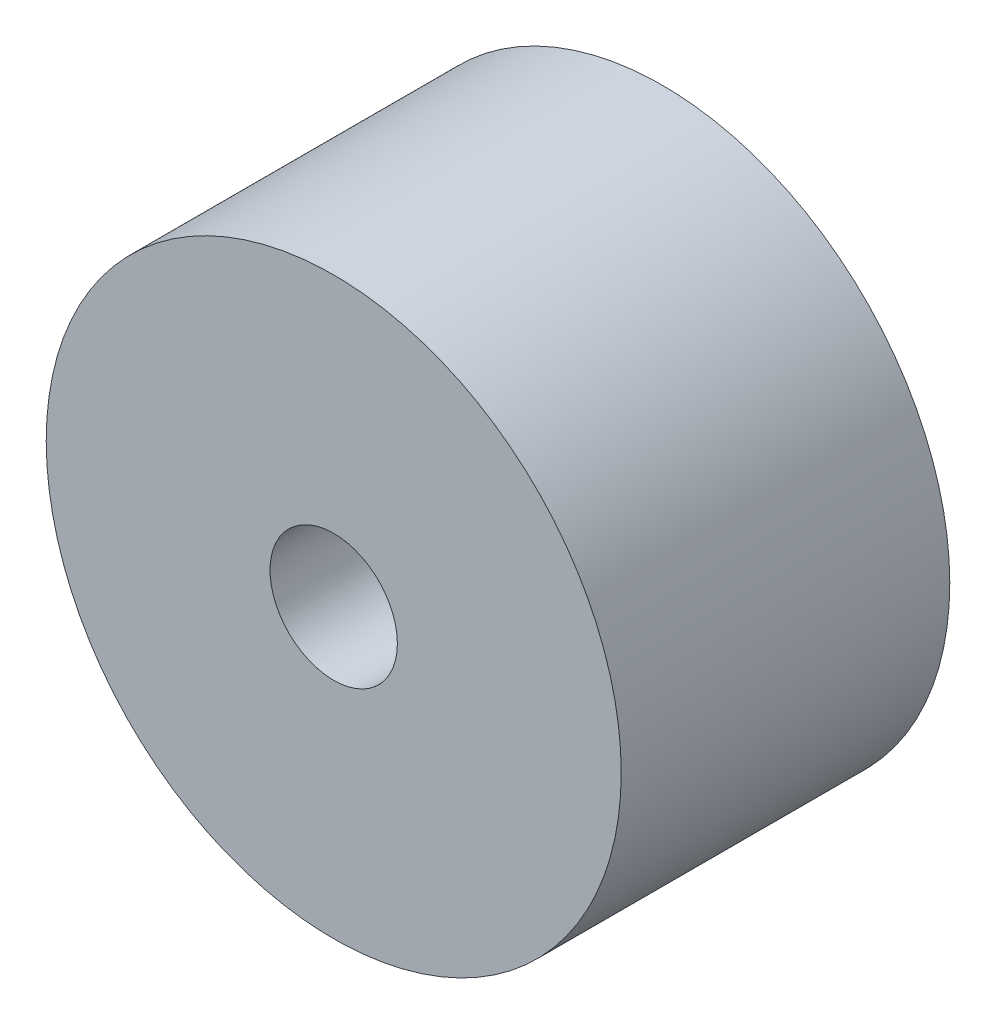
SolidWorks part; units mm, degrees
ref_plane "Front Plane" through (0, 0, 0) normal (0, 0, 1) x (1, 0, 0)
ref_plane "Top Plane" through (0, 0, 0) normal (0, 1, 0) x (1, 0, 0)
ref_plane "Right Plane" through (0, 0, 0) normal (1, 0, 0) x (0, 0, -1)
sketch "Sketch1" plane through (0, 0, 0) normal (0, 0, 1) x (1, 0, 0)
  circle A1 centre (0, 0) radius 7
  dimension "D1" = 14
extrude "Boss-Extrude1" add sketch "Sketch1" along normal blind 8
sketch "Sketch2" plane through (0, 0, 8) normal (0, 0, 1) x (1, 0, 0)
  circle A0 centre (0, 0) radius 1.55
  dimension "D1" = 3.1
extrude "Cut-Extrude1" cut sketch "Sketch2" against normal blind 3
